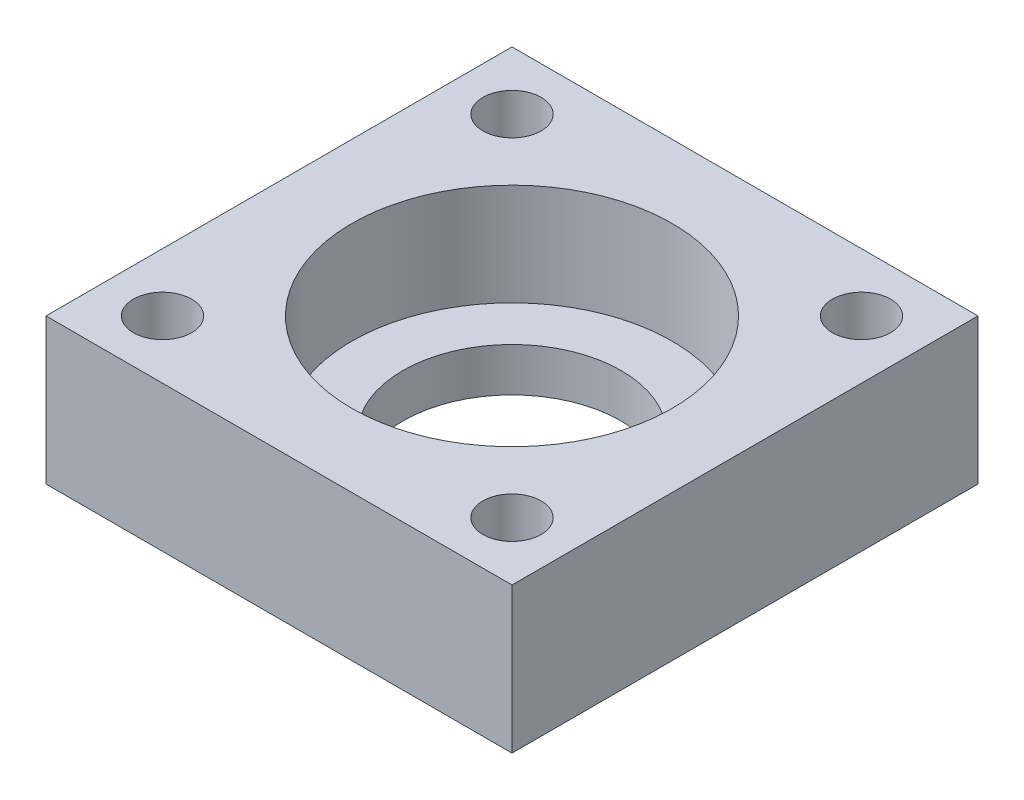
SolidWorks part; units mm, degrees
material "Chrome Stainless Steel"
ref_plane "Front Plane" through (0, 0, 0) normal (0, 0, 1) x (1, 0, 0)
ref_plane "Top Plane" through (0, 0, 0) normal (0, 1, 0) x (1, 0, 0)
ref_plane "Right Plane" through (0, 0, 0) normal (1, 0, 0) x (0, 0, -1)
sketch "Sketch1" plane through (0, 0, 0) normal (0, 1, 0) x (1, 0, 0)
  line L1 (-16, -16) -> (16, -16)
  line L2 (-16, -16) -> (-16, 16)
  line L3 (-16, 16) -> (16, 16)
  line L4 (16, -16) -> (16, 16)
  line L5 (-16, -16) -> (16, 16) construction
  line L6 (-16, 16) -> (16, -16) construction
  point P0 (0, 0)
  dimension "D1" = 32
  dimension "D2" = 32
extrude "Boss-Extrude1" add sketch "Sketch1" along normal blind 10
sketch "Sketch2" plane through (0, 10, 0) normal (0, 1, 0) x (1, 0, 0)
  line L0 (0, -7.1546) -> (0, 6.4175) construction
  line L1 (8.4988, 0) -> (-7.198, 0) construction
  circle A0 centre (0, 0) radius 11
  dimension "D1" = 22
extrude "Cut-Extrude1" cut sketch "Sketch2" against normal blind 7
sketch "Sketch3" plane through (0, 10, 0) normal (0, 1, 0) x (1, 0, 0)
  line L0 (0, -6.8684) -> (0, 5.2554) construction
  line L1 (6.9205, 0) -> (-7.0245, 0) construction
  circle A0 centre (-12, 12) radius 2
  circle A1 centre (12, 12) radius 2
  circle A2 centre (12, -12) radius 2
  circle A3 centre (-12, -12) radius 2
  circle A4 centre (0, 0) radius 7.5
  dimension "D1" = 4
  dimension "D4" = 15
  dimension "D2" = 12
  dimension "D3" = 12
extrude "Cut-Extrude2" cut sketch "Sketch3" against normal through all
